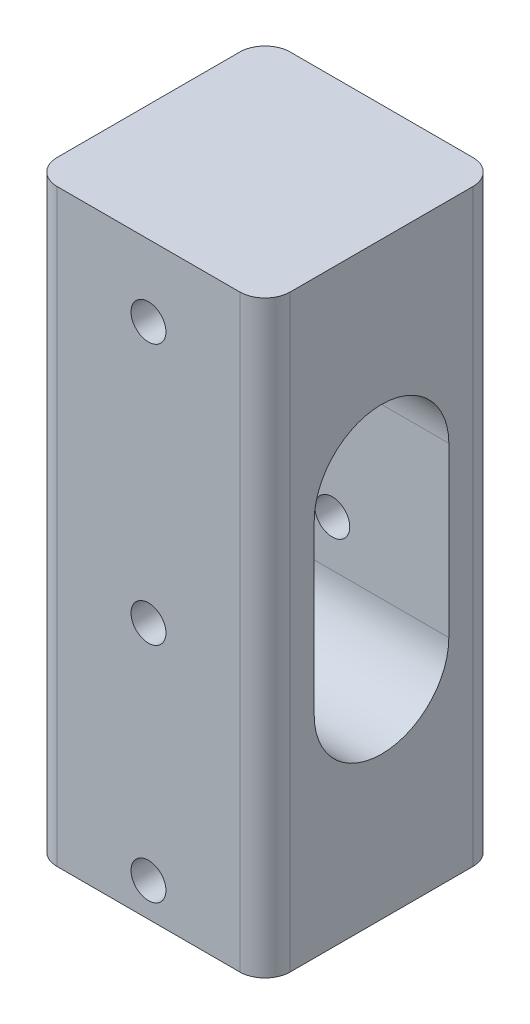
SolidWorks part; units mm, degrees
ref_plane "前视基准面" through (0, 0, 0) normal (0, 0, 1) x (1, 0, 0)
ref_plane "上视基准面" through (0, 0, 0) normal (0, 1, 0) x (1, 0, 0)
ref_plane "右视基准面" through (0, 0, 0) normal (1, 0, 0) x (0, 0, -1)
other "Configuration Table"
sketch "草图1" plane through (0, 0, 0) normal (0, 1, 0) x (1, 0, 0)
  line L1 (-13.85, -13.85) -> (13.85, -13.85)
  line L2 (-13.85, -13.85) -> (-13.85, 13.85)
  line L3 (-13.85, 13.85) -> (13.85, 13.85)
  line L4 (13.85, -13.85) -> (13.85, 13.85)
  line L5 (-13.85, -13.85) -> (13.85, 13.85) construction
  line L6 (-13.85, 13.85) -> (13.85, -13.85) construction
  point P0 (0, 0)
  dimension "D1" = 27.7
extrude "凸台-拉伸1" add sketch "草图1" along normal blind 70
sketch "草图2" plane through (0, 0, 13.85) normal (0, 0, 1) x (1, 0, 0)
  line L0 (-13.85, 0) -> (13.85, 0) construction
  circle A0 centre (0, 4) radius 2.075
  circle A1 centre (0, 30.5) radius 2.075
  circle A2 centre (0, 61.5) radius 2.075
  point P8 (0, 0)
  dimension "D1" = 4.15
  dimension "D2" = 26.5
  dimension "D3" = 31
  dimension "D4" = 4
extrude "切除-拉伸1" cut sketch "草图2" against normal blind 70
sketch "草图3" plane through (-13.85, 0, 0) normal (-1, 0, 0) x (0, 0, 1)
  line L0 (0, 25) -> (0, 45) construction
  line L1 (-8, 25) -> (-8, 45)
  line L2 (8, 25) -> (8, 45)
  line L3 (-13.85, 0) -> (13.85, 0) construction
  line L4 (-13.85, 70) -> (13.85, 70) construction
  arc A0 (-8, 25) -> (8, 25) centre (0, 25) ccw
  arc A1 (8, 45) -> (-8, 45) centre (0, 45) ccw
  point P3 (0, 35)
  dimension "D1" = 8
  dimension "D3" = 25
  dimension "D2" = 25
extrude "切除-拉伸2" cut sketch "草图3" against normal blind 70
fillet "圆角1" radius 3 4 edges at (13.85, 35, 13.85) (-13.85, 35, -13.85) (13.85, 35, -13.85) (-13.85, 35, 13.85)
